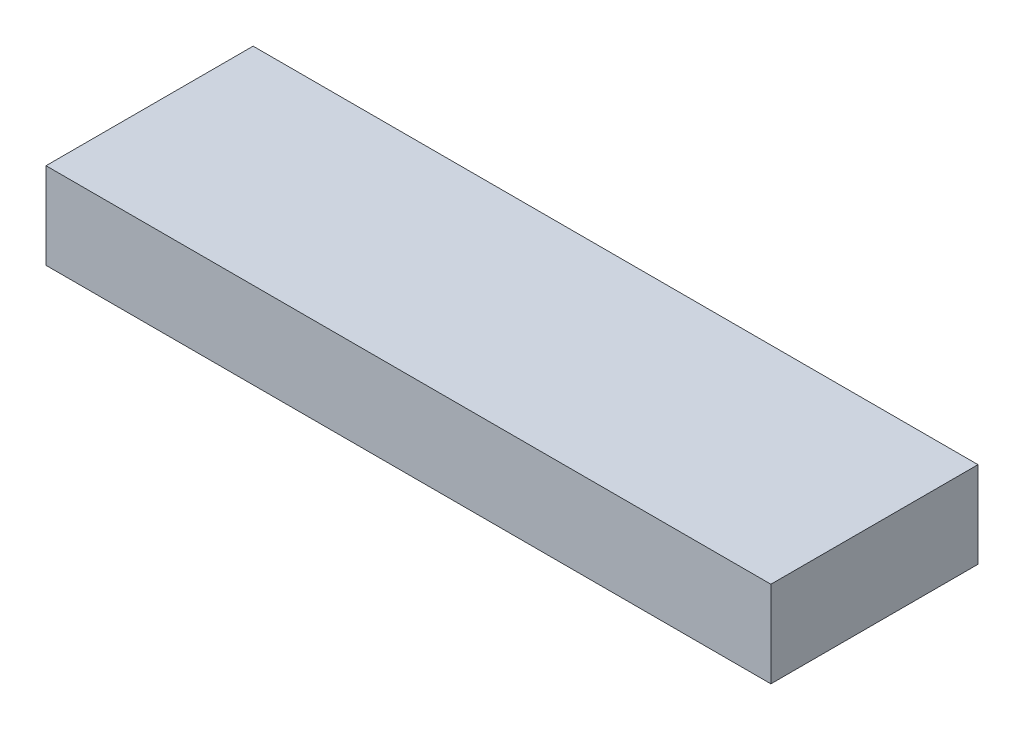
SolidWorks part; units mm, degrees
material "Plain Carbon Steel"
ref_plane "Front Plane" through (0, 0, 0) normal (0, 0, 1) x (1, 0, 0)
ref_plane "Top Plane" through (0, 0, 0) normal (0, 1, 0) x (1, 0, 0)
ref_plane "Right Plane" through (0, 0, 0) normal (1, 0, 0) x (0, 0, -1)
sketch "Sketch1" plane through (0, 0, 0) normal (0, 1, 0) x (1, 0, 0)
  line L1 (-105, -30) -> (105, -30)
  line L2 (-105, -30) -> (-105, 30)
  line L3 (-105, 30) -> (105, 30)
  line L4 (105, -30) -> (105, 30)
  line L5 (-105, -30) -> (105, 30) construction
  line L6 (-105, 30) -> (105, -30) construction
  point P0 (0, 0)
  dimension "D1" = 60
  dimension "D2" = 210
extrude "Boss-Extrude1" add sketch "Sketch1" along normal blind 25
